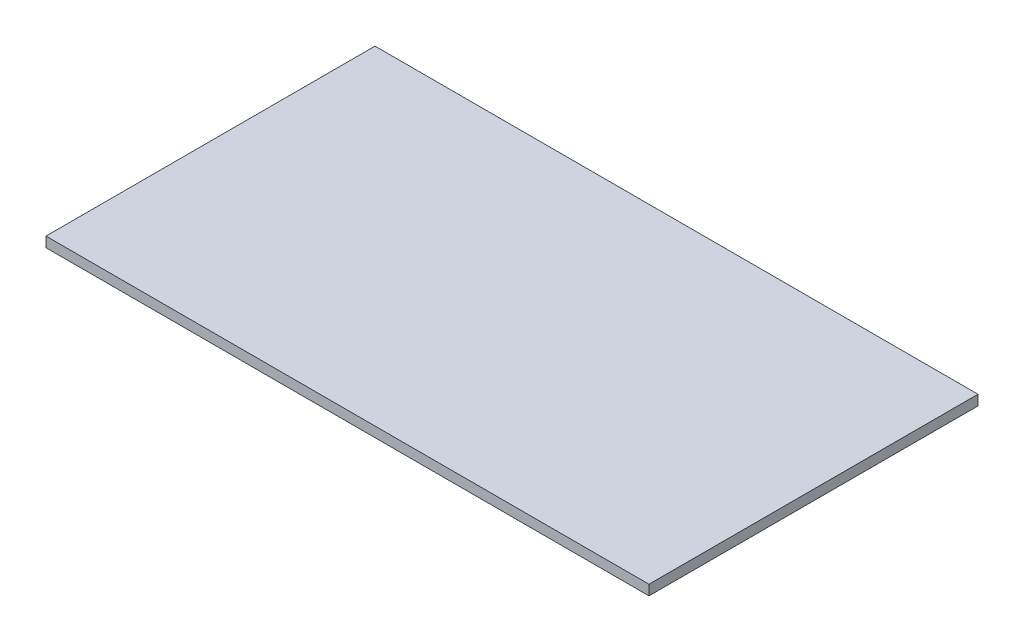
SolidWorks part; units mm, degrees
ref_plane "Front Plane" through (0, 0, 0) normal (0, 0, 1) x (1, 0, 0)
ref_plane "Top Plane" through (0, 0, 0) normal (0, 1, 0) x (1, 0, 0)
ref_plane "Right Plane" through (0, 0, 0) normal (1, 0, 0) x (0, 0, -1)
sketch "Sketch1" plane through (0, 0, 0) normal (0, 1, 0) x (1, 0, 0)
  line L1 (-59.6, -32.52) -> (59.6, -32.52)
  line L2 (-59.6, -32.52) -> (-59.6, 32.52)
  line L3 (-59.6, 32.52) -> (59.6, 32.52)
  line L4 (59.6, -32.52) -> (59.6, 32.52)
  line L5 (-59.6, -32.52) -> (59.6, 32.52) construction
  line L6 (-59.6, 32.52) -> (59.6, -32.52) construction
  point P0 (0, 0)
  dimension "D1" = 119.2
  dimension "D2" = 65.04
extrude "Boss-Extrude1" add sketch "Sketch1" along normal blind 2
ref_plane "Plane1" through (0, 0, 0) normal (-1, 0, 0) x (0, 0, 1)
